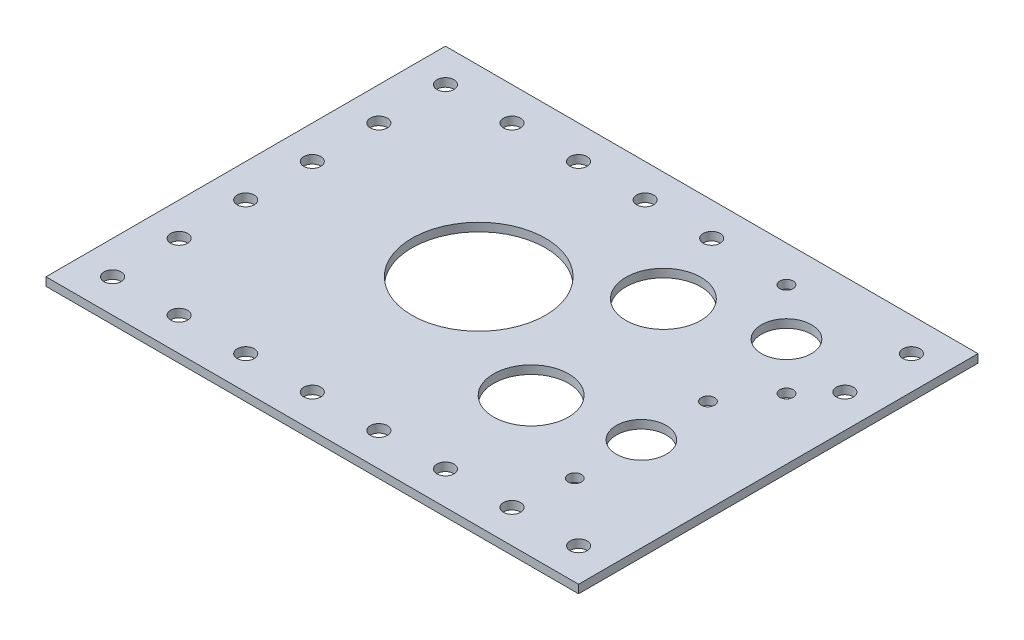
SolidWorks part; units mm, degrees
material "6061 Alloy"
ref_plane "Front Plane" through (0, 0, 0) normal (0, 0, 1) x (1, 0, 0)
ref_plane "Top Plane" through (0, 0, 0) normal (0, 1, 0) x (1, 0, 0)
ref_plane "Right Plane" through (0, 0, 0) normal (1, 0, 0) x (0, 0, -1)
sketch "Sketch1" plane through (0, 0, 0) normal (0, 1, 0) x (1, 0, 0)
  line L1 (0, 0) -> (203.2, 0)
  line L2 (0, 0) -> (0, 152.4)
  line L3 (0, 152.4) -> (203.2, 152.4)
  line L4 (203.2, 0) -> (203.2, 152.4)
extrude "Boss-Extrude1" add sketch "Sketch1" along normal blind 3.175
sketch "Sketch2" plane through (0, 3.175, 0) normal (0, 1, 0) x (1, 0, 0)
  circle A0 centre (82.55, 82.55) radius 25.4762
  circle A7 centre (131.7498, 53.34) radius 14.2875
  circle A8 centre (167.4622, 59.69) radius 9.525
  circle A9 centre (167.4622, 34.29) radius 2.54
  circle A10 centre (167.4622, 85.09) radius 2.54
  circle A11 centre (125.0696, 110.49) radius 14.2875
  circle A12 centre (161.8742, 120.65) radius 9.5504
  circle A13 centre (179.832, 102.6922) radius 2.54
  circle A14 centre (143.9164, 138.6078) radius 2.54
  point P16 (82.55, 82.55)
sketch "Sketch3" plane through (0, 3.175, 0) normal (0, 1, 0) x (1, 0, 0)
  circle A0 centre (12.7, 12.7) radius 3.2512
  circle A2 centre (38.1, 12.7) radius 3.2512
  circle A4 centre (63.5, 12.7) radius 3.2512
  circle A6 centre (88.9, 12.7) radius 3.2512
  circle A8 centre (114.3, 12.7) radius 3.2512
  circle A10 centre (139.7, 12.7) radius 3.2512
  circle A12 centre (165.1, 12.7) radius 3.2512
  circle A14 centre (190.5, 12.7) radius 3.2512
  circle A22 centre (190.5, 114.3) radius 3.2512
  circle A24 centre (190.5, 139.7) radius 3.2512
  circle A26 centre (12.7, 38.1) radius 3.2512
  circle A28 centre (12.7, 63.5) radius 3.2512
  circle A30 centre (12.7, 88.9) radius 3.2512
  circle A32 centre (12.7, 114.3) radius 3.2512
  circle A34 centre (12.7, 139.7) radius 3.2512
  circle A36 centre (38.1, 139.7) radius 3.2512
  circle A38 centre (63.5, 139.7) radius 3.2512
  circle A40 centre (88.9, 139.7) radius 3.2512
  circle A42 centre (114.3, 139.7) radius 3.2512
  circle A48 centre (139.7, 139.7) radius 3.2512 [skipped]
  circle A49 centre (152.4, 139.7) radius 3.2512 [skipped]
  circle A50 centre (165.1, 139.7) radius 3.2512 [skipped]
  circle A51 centre (177.8, 139.7) radius 3.2512 [skipped]
  circle A52 centre (190.5, 76.2) radius 3.2512 [skipped]
  circle A53 centre (190.5, 63.5) radius 3.2512 [skipped]
  circle A54 centre (190.5, 50.8) radius 3.2512 [skipped]
  circle A55 centre (190.5, 38.1) radius 3.2512 [skipped]
  circle A56 centre (190.5, 101.6) radius 3.2512 [skipped]
  circle A57 centre (190.5, 127) radius 3.2512 [skipped]
  circle A58 centre (190.5, 88.9) radius 3.2512 [skipped]
  circle A59 centre (190.5, 25.4) radius 3.2512 [skipped]
  circle A60 centre (177.8, 12.7) radius 3.2512 [skipped]
  circle A61 centre (152.4, 12.7) radius 3.2512 [skipped]
  circle A62 centre (127, 12.7) radius 3.2512 [skipped]
  circle A63 centre (101.6, 12.7) radius 3.2512 [skipped]
  circle A64 centre (76.2, 12.7) radius 3.2512 [skipped]
  circle A65 centre (50.8, 12.7) radius 3.2512 [skipped]
  circle A66 centre (25.4, 12.7) radius 3.2512 [skipped]
  circle A67 centre (12.7, 25.4) radius 3.2512 [skipped]
  circle A68 centre (12.7, 50.8) radius 3.2512 [skipped]
  circle A69 centre (12.7, 76.2) radius 3.2512 [skipped]
  circle A70 centre (12.7, 101.6) radius 3.2512 [skipped]
  circle A71 centre (12.7, 127) radius 3.2512 [skipped]
  circle A72 centre (25.4, 139.7) radius 3.2512 [skipped]
  circle A73 centre (50.8, 139.7) radius 3.2512 [skipped]
  circle A74 centre (76.2, 139.7) radius 3.2512 [skipped]
  circle A75 centre (101.6, 139.7) radius 3.2512 [skipped]
  circle A76 centre (127, 139.7) radius 3.2512 [skipped]
  dimension "D1" = 15
  dimension "D2" = 11
  dimension "D3" = 11
  dimension "D4" = 14
extrude "Cut-Extrude4" cut sketch "Sketch3" against normal blind 5.08
extrude "Cut-Extrude5" cut sketch "Sketch2" against normal blind 50.8
